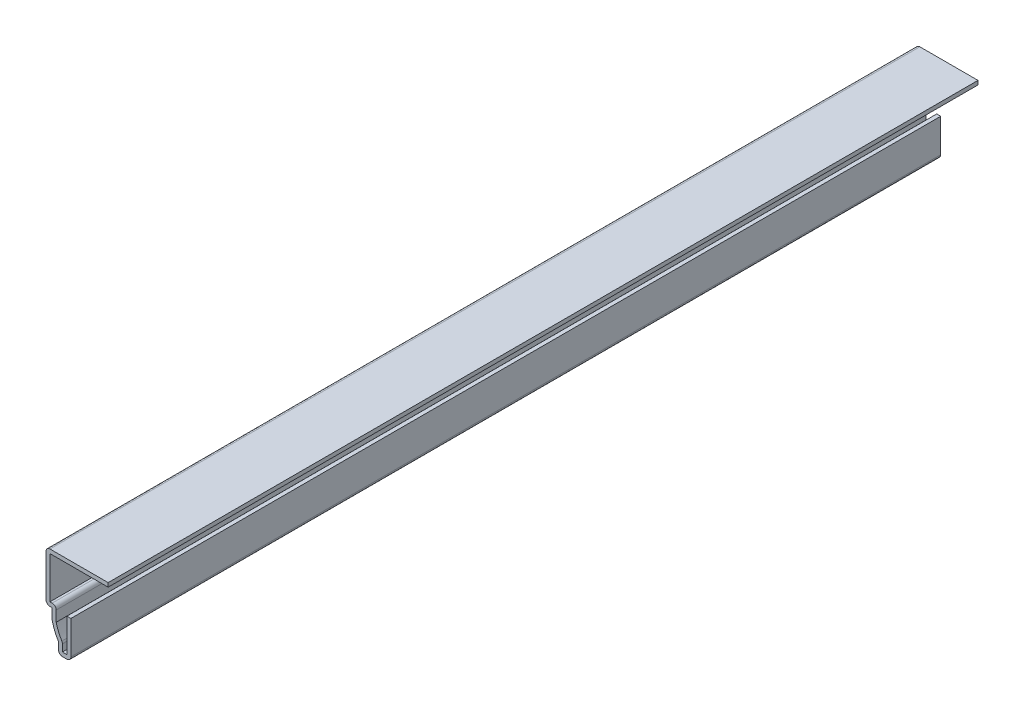
SolidWorks part; units mm, degrees
ref_plane "Front Plane" through (0, 0, 0) normal (0, 0, 1) x (1, 0, 0)
ref_plane "Top Plane" through (0, 0, 0) normal (0, 1, 0) x (1, 0, 0)
ref_plane "Right Plane" through (0, 0, 0) normal (1, 0, 0) x (0, 0, -1)
sketch "Sketch1" plane through (0, 0, 0) normal (0, 0, 1) x (1, 0, 0)
  line L0 (0, 0) -> (0, -9.525)
  line L1 (0, -9.525) -> (-3.175, -9.525)
  line L2 (-3.175, -9.525) -> (-3.175, -6.6936)
  line L3 (-4.7625, -2.8314) -> (-4.7625, 0)
  line L4 (-4.7625, 0) -> (-6.35, 0)
  line L5 (-6.35, 0) -> (-6.35, 12.7)
  line L6 (-6.35, 12.7) -> (9.525, 12.7)
  arc A0 (-4.7625, -2.8314) -> (-3.175, -6.6936) centre (7.6179, 0) ccw
  point P7 (-3.175, -6.9266)
  point P12 (0, 0)
  dimension "D3" = 12.7
  dimension "D1" = 9.525
  dimension "D2" = 3.175
  dimension "D4" = 1.5875
  dimension "D5" = 1.5875
  dimension "D6" = 12.7
  dimension "D7" = 15.875
  dimension "D8" = 22.225
extrude "Extrude-Thin1" add sketch "Sketch1" against normal blind 222.25 thin
fillet "Fillet1" radius 1.016 7 edges at (0, -9.525, -111.125) (-3.175, -9.525, -111.125) (-3.7465, 1.016, -111.125) (-6.35, 0, -111.125) (-6.35, 12.7, -111.125) (-2.159, -6.3976, -111.125) (-4.7625, -2.8314, -111.125)
